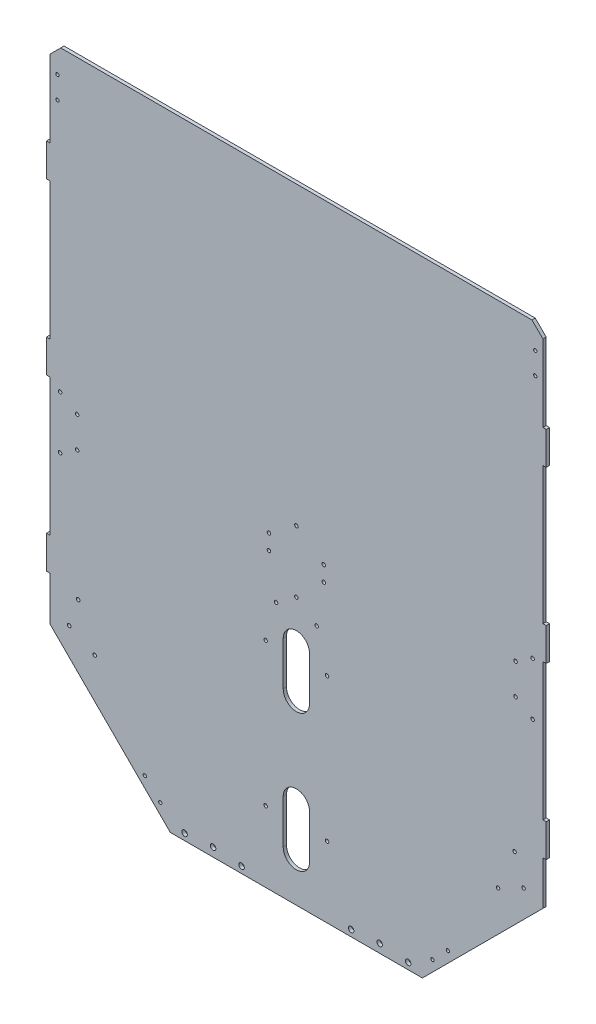
SolidWorks part; units mm, degrees
material "Acrylic (Medium-high impact)"
ref_plane "前视基准面" through (0, 0, 0) normal (0, 0, 1) x (1, 0, 0)
ref_plane "上视基准面" through (0, 0, 0) normal (0, 1, 0) x (1, 0, 0)
ref_plane "右视基准面" through (0, 0, 0) normal (1, 0, 0) x (0, 0, -1)
sketch "草图1" plane through (0, 0, 0) normal (0, 0, 1) x (1, 0, 0)
  line L0 (-225, 205) -> (-228, 205)
  line L1 (-225, 285) -> (225, 285)
  line L2 (-225, 285) -> (-225, 205)
  line L3 (-225, -285) -> (225, -285)
  line L4 (225, 285) -> (225, 205)
  line L5 (-225, 285) -> (225, -285) construction
  line L6 (-225, -285) -> (225, 285) construction
  line L7 (-228, 205) -> (-228, 175)
  line L8 (-228, 175) -> (-225, 175)
  line L9 (-225, 175) -> (-225, 50)
  line L10 (-225, 50) -> (-228, 50)
  line L11 (-228, 50) -> (-228, 20)
  line L12 (-228, 20) -> (-225, 20)
  line L13 (-225, -105) -> (-228, -105)
  line L14 (-228, -105) -> (-228, -135)
  line L15 (-228, -135) -> (-225, -135)
  line L16 (-225, 20) -> (-225, -105)
  line L17 (-225, -135) -> (-225, -285)
  line L18 (0, 0) -> (0, 121.9272) construction
  line L19 (225, -105) -> (228, -105)
  line L20 (228, -105) -> (228, -135)
  line L21 (228, -135) -> (225, -135)
  line L22 (225, 50) -> (228, 50)
  line L23 (228, 50) -> (228, 20)
  line L24 (228, 20) -> (225, 20)
  line L25 (225, 205) -> (228, 205)
  line L26 (228, 205) -> (228, 175)
  line L27 (228, 175) -> (225, 175)
  line L28 (225, -135) -> (225, -285)
  line L29 (225, 20) -> (225, -105)
  line L30 (225, 175) -> (225, 50)
  point P0 (0, 0)
  dimension "D1" = 450
  dimension "D2" = 570
  dimension "D3" = 30
  dimension "D4" = 3
  dimension "D5" = 80
  dimension "D6" = 3
  dimension "D7" = 30
  dimension "D8" = 30
  dimension "D9" = 3
  dimension "D10" = 150
extrude "凸台-拉伸1" add sketch "草图1" along normal blind 3
chamfer "Chamfer1" distance 110 angle 45 2 edges at (-225, -285, 1.5) (225, -285, 1.5)
sketch "Sketch1" plane through (0, 0, 0) normal (0, 0, -1) x (-1, 0, 0)
  circle A0 centre (102, -279.1) radius 2.5 construction
  circle A1 centre (76, -277.1) radius 2.5 construction
  circle A2 centre (50, -279.1) radius 2.5 construction
  circle A3 centre (-50, -279.1) radius 2.5 construction
  circle A4 centre (-76, -277.1) radius 2.5 construction
  circle A5 centre (-102, -279.1) radius 2.5 construction
  circle A6 centre (102, -279.1) radius 2.5
  circle A7 centre (76, -277.1) radius 2.5
  circle A8 centre (50, -279.1) radius 2.5
  circle A9 centre (-50, -279.1) radius 2.5
  circle A10 centre (-76, -277.1) radius 2.5
  circle A11 centre (-102, -279.1) radius 2.5
extrude "Cut-Extrude1" cut sketch "Sketch1" against normal blind 10
sketch "Sketch2" plane through (0, 0, 3) normal (0, 0, 1) x (1, 0, 0)
  circle A0 centre (18.5, -55) radius 1.6 construction
  circle A1 centre (-18.5, -55) radius 1.6 construction
  circle A2 centre (0, -41.5) radius 1.6 construction
  circle A3 centre (18.5, -55) radius 1.6
  circle A4 centre (-18.5, -55) radius 1.6
  circle A5 centre (0, -41.5) radius 1.6
extrude "Cut-Extrude2" cut sketch "Sketch2" against normal blind 10
sketch "Sketch3" plane through (0, 0, 3) normal (0, 0, 1) x (1, 0, 0)
  line L0 (0, -245) -> (0, -205) construction
  line L1 (-12, -245) -> (-12, -205)
  line L2 (12, -245) -> (12, -205)
  line L3 (0, -120) -> (0, -80) construction
  line L4 (-12, -120) -> (-12, -80)
  line L5 (12, -120) -> (12, -80)
  line L6 (-115, -285) -> (115, -285) construction
  arc A0 (-12, -245) -> (12, -245) centre (0, -245) ccw
  arc A1 (12, -205) -> (-12, -205) centre (0, -205) ccw
  arc A2 (-12, -120) -> (12, -120) centre (0, -120) ccw
  arc A3 (12, -80) -> (-12, -80) centre (0, -80) ccw
  point P3 (0, -225)
  point P8 (0, -100)
  dimension "D4" = 12
  dimension "D1" = 40
  dimension "D2" = 185
  dimension "D3" = 60
extrude "Cut-Extrude3" cut sketch "Sketch3" against normal blind 10
sketch "Sketch4" plane through (0, 0, 3) normal (0, 0, 1) x (1, 0, 0)
  line L0 (0, 285) -> (0, -285) construction
  line L1 (225, 285) -> (-225, 285) construction
  line L2 (-115, -285) -> (115, -285) construction
  circle A0 centre (184.0621, -179.3169) radius 1.6 construction
  circle A1 centre (207.2895, -167.6641) radius 1.6 construction
  circle A2 centre (199.105, -143) radius 1.6 construction
  circle A3 centre (215.5711, -30.2175) radius 1.6 construction
  circle A4 centre (200, -20.2175) radius 1.6 construction
  circle A5 centre (200, 7.8895) radius 1.6 construction
  circle A6 centre (215.5711, 17.8895) radius 1.6 construction
  circle A7 centre (184.0621, -179.3169) radius 1.6
  circle A8 centre (207.2895, -167.6641) radius 1.6
  circle A9 centre (199.105, -143) radius 1.6
  circle A10 centre (215.5711, -30.2175) radius 1.6
  circle A11 centre (200, -20.2175) radius 1.6
  circle A12 centre (200, 7.8895) radius 1.6
  circle A13 centre (215.5711, 17.8895) radius 1.6
  circle A14 centre (-215.5711, 12.8704) radius 1.6
  circle A15 centre (-200, 2.8704) radius 1.6
  circle A16 centre (-200, -25.2366) radius 1.6
  circle A17 centre (-215.5711, -35.2366) radius 1.6
  circle A18 centre (-199.105, -143) radius 1.6
  circle A19 centre (-207.2895, -167.6641) radius 1.6
  circle A20 centre (-184.0621, -179.3169) radius 1.6
  point P41 (-215.5711, 12.8704)
  point P43 (-200, 2.8704)
  point P45 (-200, -25.2366)
  point P47 (-215.5711, -35.2366)
extrude "Cut-Extrude4" cut sketch "Sketch4" against normal blind 8
sketch "Sketch5" plane through (0, 0, 3) normal (0, 0, 1) x (1, 0, 0)
  line L0 (0, 285) -> (0, 211.9494) construction
  line L1 (225, 285) -> (-225, 285) construction
  circle A0 centre (124.1924, -265.9081) radius 1.5 construction
  circle A1 centre (138.3345, -251.766) radius 1.5 construction
  circle A2 centre (218, 242.3615) radius 1.5 construction
  circle A3 centre (218, 262.3615) radius 1.5 construction
  circle A4 centre (124.1924, -265.9081) radius 1.5
  circle A5 centre (138.3345, -251.766) radius 1.5
  circle A6 centre (218, 242.3615) radius 1.5
  circle A7 centre (218, 262.3615) radius 1.5
  circle A8 centre (-218, 262.3615) radius 1.5
  circle A9 centre (-218, 242.3615) radius 1.5
  circle A10 centre (-138.3345, -251.766) radius 1.5
  circle A11 centre (-124.1924, -265.9081) radius 1.5
extrude "Cut-Extrude5" cut sketch "Sketch5" against normal blind 3
sketch "Sketch6" plane through (0, 0, 0) normal (0, 0, -1) x (-1, 0, 0)
  circle A4 centre (-28, -89.6188) radius 1.6
  circle A5 centre (28, -89.6188) radius 1.6
  circle A6 centre (28, -220.3812) radius 1.6
  circle A7 centre (-28, -220.3812) radius 1.6
extrude "Cut-Extrude6" cut sketch "Sketch6" against normal blind 3
chamfer "Chamfer2" distance 10 angle 45 2 edges at (225, 285, 1.5) (-225, 285, 1.5)
sketch "Sketch7" plane through (0, 0, 3) normal (0, 0, 1) x (1, 0, 0)
  circle A0 centre (25, -17.2366) radius 1.6 construction
  circle A1 centre (25, -3.3428) radius 1.6 construction
  circle A2 centre (0, 14.8704) radius 1.6 construction
  circle A3 centre (-25, -17.2366) radius 1.6 construction
  circle A4 centre (-25, -3.3428) radius 1.6 construction
  circle A5 centre (25, -17.2366) radius 1.6
  circle A6 centre (25, -3.3428) radius 1.6
  circle A7 centre (0, 14.8704) radius 1.6
  circle A8 centre (-25, -17.2366) radius 1.6
  circle A9 centre (-25, -3.3428) radius 1.6
extrude "Cut-Extrude7" cut sketch "Sketch7" against normal blind 10
